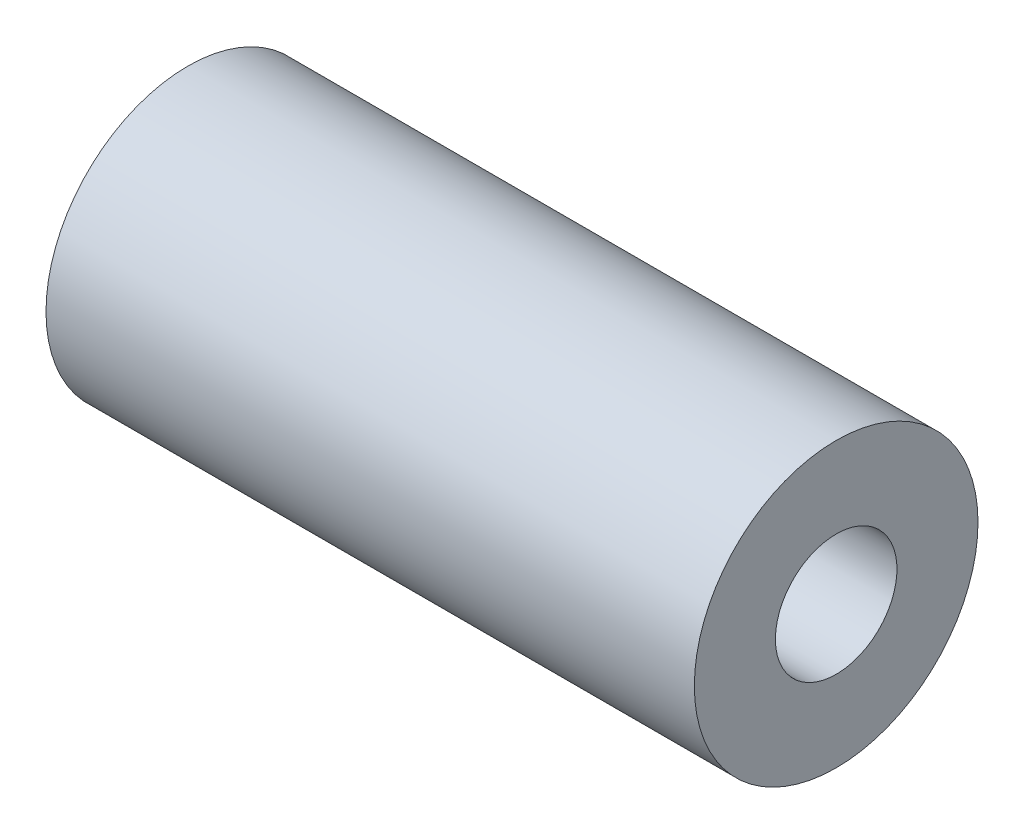
SolidWorks part; units mm, degrees
material "POM Acetal Copolymer"
ref_plane "Front Plane" through (0, 0, 0) normal (0, 0, 1) x (1, 0, 0)
ref_plane "Top Plane" through (0, 0, 0) normal (0, 1, 0) x (1, 0, 0)
ref_plane "Right Plane" through (0, 0, 0) normal (1, 0, 0) x (0, 0, -1)
sketch "Sketch1" plane through (0, 0, 0) normal (0, 0, 1) x (1, 0, 0)
  line L0 (-37.0032, 0) -> (16, 0) construction
  line L1 (-16, 7) -> (16, 7)
  line L2 (-16, 7) -> (-16, 3)
  line L3 (-16, 3) -> (16, 3)
  line L4 (16, 7) -> (16, 3)
  line L5 (16, 0) -> (16, 3) construction
  line L6 (0, 0) -> (0, 7) construction
  dimension "D1" = 6
  dimension "D2" = 32
  dimension "D3" = 14
revolve "Revolve1" add sketch "Sketch1" angle 360 about L0
